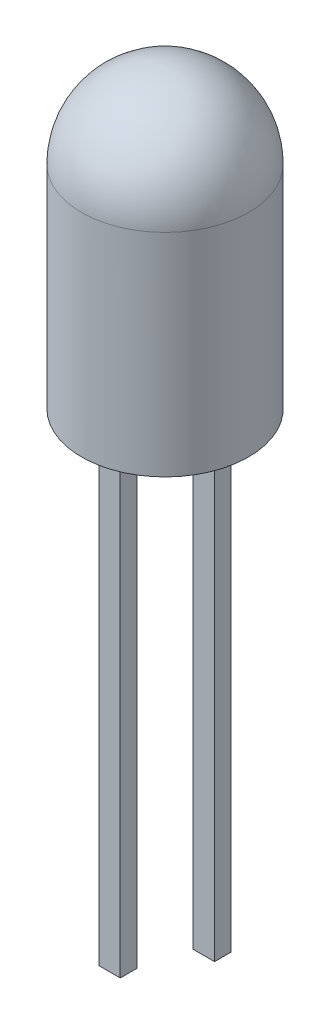
SolidWorks part; units mm, degrees
ref_plane "Front Plane" through (0, 0, 0) normal (0, 0, 1) x (1, 0, 0)
ref_plane "Top Plane" through (0, 0, 0) normal (0, 1, 0) x (1, 0, 0)
ref_plane "Right Plane" through (0, 0, 0) normal (1, 0, 0) x (0, 0, -1)
sketch "Sketch1" plane through (0, 0, 0) normal (0, 0, 1) x (1, 0, 0)
  line L0 (0, 0) -> (0, 27.4114) construction
  line L1 (0, 0) -> (-1.5, 0)
  line L4 (-1.5, 5.3) -> (-6.2879, 5.3) construction
  line L5 (-1.5, 0) -> (-1.5, 3.8)
  line L6 (0, 0) -> (0, 5.3)
  arc A0 (-1.5, 3.8) -> (0, 5.3) centre (0, 3.8) cw
  point P9 (-1.5, 3.8)
  dimension "D6" = 1.5
  dimension "D4" = 5.3
  dimension "D7" = 5.3
revolve "Revolve1" add sketch "Sketch1" angle 360 about L6
sketch "Sketch3" plane through (0, 0, 0) normal (0, -1, 0) x (1, 0, 0)
  line L0 (1.5, 0) -> (-1.5, 0) construction
  line L4 (-1.0379, 0.1492) -> (-0.6548, 0.1492)
  line L5 (-1.0379, 0.1492) -> (-1.0379, -0.1492)
  line L6 (-1.0379, -0.1492) -> (-0.6548, -0.1492)
  line L7 (-0.6548, 0.1492) -> (-0.6548, -0.1492)
  line L8 (-1.0379, 0.1492) -> (-0.6548, -0.1492) construction
  line L9 (-1.0379, -0.1492) -> (-0.6548, 0.1492) construction
  line L10 (1.0379, 0.1492) -> (0.6548, 0.1492)
  line L11 (1.0379, 0.1492) -> (1.0379, -0.1492)
  line L12 (1.0379, -0.1492) -> (0.6548, -0.1492)
  line L13 (0.6548, 0.1492) -> (0.6548, -0.1492)
  line L14 (1.0379, 0.1492) -> (0.6548, -0.1492) construction
  line L15 (1.0379, -0.1492) -> (0.6548, 0.1492) construction
  circle A1 centre (0, 0) radius 1.5 construction
  point P3 (0.8463, 0)
  point P9 (-0.8463, 0)
  dimension "D1" = 0.3831
  dimension "D2" = 0.3831
  dimension "D3" = 0.2985
  dimension "D4" = 0.2985
  dimension "D5" = 0.6548
  dimension "D6" = 0.6548
extrude "Boss-Extrude1" add sketch "Sketch3" along normal blind 8 separate body
sketch "Sketch4" plane through (0, 0, 0) normal (0, 0, 1) x (1, 0, 0)
  line L0 (1.0379, 2.2604) -> (0.2941, 2.7888)
  line L1 (-0.5659, 2.6172) -> (-0.5659, 2.7967)
  line L2 (-1.0379, -0.4146) -> (-1.0379, 2.5705) construction
  line L3 (-1.0379, -8) -> (-1.0379, 0) construction
  line L4 (1.0379, -0.4738) -> (1.0379, 2.2604) construction
  line L5 (1.0379, -8) -> (1.0379, 0) construction
  line L6 (0.4821, 1.5513) -> (-0.6659, 2.3668)
  line L7 (1.1181, 2.2034) -> (-0.1026, 3.0706) construction
  line L8 (1.0379, 2.2604) -> (1.0379, 1.5513)
  line L9 (0.4821, 1.5513) -> (-0.6548, 1.5513)
  line L10 (-1.0379, 2.6172) -> (-1.0379, 1.5513)
  line L12 (-0.3857, 2.7069) -> (0.236, 2.7069)
  line L13 (-0.6659, 2.6172) -> (-0.6659, 2.3668)
  line L14 (-0.5659, 2.6172) -> (-0.5659, 2.4185)
  line L15 (0.6548, 1.5513) -> (-0.5659, 2.4185)
  line L16 (0.5969, 1.4697) -> (-0.6659, 2.3668) construction
  line L17 (0.6548, 0) -> (0.6548, 1.5513) construction
  line L18 (0.6548, 1.5513) -> (0.6548, 0)
  line L19 (1.0379, 1.5513) -> (1.0379, 0)
  line L20 (1.0379, 0) -> (0.6548, 0)
  line L21 (-1.0379, 1.5513) -> (-1.0379, 0)
  line L22 (-0.6548, 0) -> (-0.6548, 1.5513)
  line L23 (-1.0379, 0) -> (-0.6548, 0)
  line L24 (-0.6659, 2.6172) -> (-1.0379, 2.6172)
  line L25 (0.236, 2.7069) -> (0.2941, 2.7888)
  line L26 (-0.5659, 2.7967) -> (-0.5127, 2.7967)
  line L27 (-0.5127, 2.7967) -> (-0.3857, 2.7069)
  point P13 (0, 2.0842)
  dimension "D1" = 0.1
  dimension "D2" = 0.8
extrude "Boss-Extrude2" add sketch "Sketch4" along normal mid plane 0.3
sketch "Sketch5" plane through (0, 2.7069, 0) normal (0, 1, 0) x (1, 0, 0)
  circle A0 centre (-0.0606, 0) radius 0.1894
extrude "Boss-Extrude3" add sketch "Sketch5" along normal blind 0.1 separate body
sketch "Sketch7" plane through (0, -8, 0) normal (0, -1, 0) x (1, 0, 0)
  line L4 (-0.6548, -0.1492) -> (-0.6548, 0.1492)
  line L5 (-0.6548, 0.1492) -> (-1.0379, 0.1492)
  line L6 (-1.0379, 0.1492) -> (-1.0379, -0.1492)
  line L7 (-1.0379, -0.1492) -> (-0.6548, -0.1492)
  line L8 (-0.6548, -0.1492) -> (-0.6548, 0.1492)
  line L9 (-0.6548, 0.1492) -> (-1.0379, 0.1492)
  line L10 (-1.0379, 0.1492) -> (-1.0379, -0.1492)
  line L11 (-1.0379, -0.1492) -> (-0.6548, -0.1492)
  dimension "D1" = 0
extrude "Boss-Extrude5" add sketch "Sketch7" along normal blind 1.1
